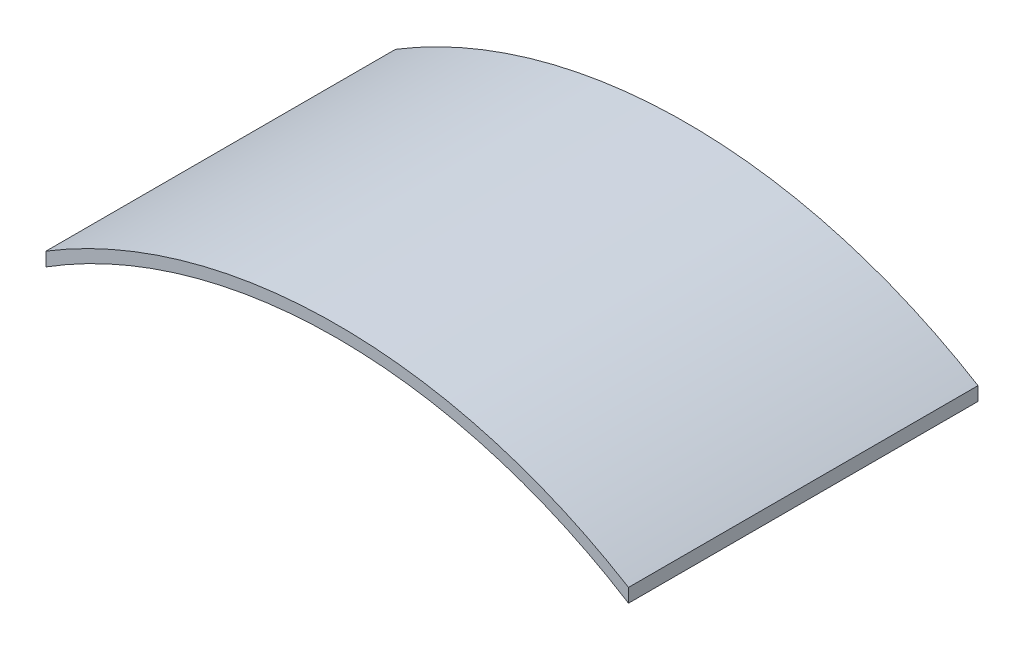
SolidWorks part; units mm, degrees
ref_plane "Front Plane" through (0, 0, 0) normal (0, 0, 1) x (1, 0, 0)
ref_plane "Top Plane" through (0, 0, 0) normal (0, 1, 0) x (1, 0, 0)
ref_plane "Right Plane" through (0, 0, 0) normal (1, 0, 0) x (0, 0, -1)
sketch "Sketch5" plane through (0, 0, 0) normal (0, 1, 0) x (1, 0, 0)
  line L1 (25, 15) -> (-25, 15)
  line L2 (25, 15) -> (25, -15)
  line L3 (25, -15) -> (-25, -15)
  line L4 (-25, 15) -> (-25, -15)
  line L5 (25, 15) -> (-25, -15) construction
  line L6 (25, -15) -> (-25, 15) construction
  point P0 (0, 0)
  dimension "D1" = 30
  dimension "D2" = 50
sketch "Sketch8" plane through (0, 0, 0) normal (0, 0, 1) x (1, 0, 0)
  circle A0 centre (0, 0) radius 50
  dimension "D1" = 100
ref_plane "Plane2" through (0, 0, 15) normal (0, 0, 1) x (1, 0, 0)
ref_plane "Plane3" through (0, 0, -15) normal (0, 0, 1) x (1, 0, 0)
curve "Curve1"
sketch "Sketch12" plane through (0, 0, 0) normal (0, 0, 1) x (1, 0, 0)
  line L0 (0, 0) -> (-84.213, 0) construction
  line L1 (16.5, 0) -> (-16.5, 0) construction
  line L2 (-84.213, 0) -> (69.4469, 0) construction
  line L3 (-48, 0) -> (-47, 0)
  line L4 (47, 0) -> (48, 0)
  arc A0 (48, 0) -> (-48, 0) centre (0, 0) ccw
  arc A1 (47, 0) -> (-47, 0) centre (0, 0) ccw
  dimension "D1" = 94
  dimension "D2" = 47
  dimension "D3" = 48
extrude "Boss-Extrude2" add sketch "Sketch12" along normal blind 30
ref_plane "Plane4" through (0, 60, 0) normal (0, 1, 0) x (1, 0, 0)
sketch "Sketch13" plane through (0, 60, 0) normal (0, 1, 0) x (1, 0, 0)
  line L0 (54.4331, -15) -> (-59.9832, -15) construction
  line L1 (-59.4484, -15) -> (59.4484, -15) construction
  line L2 (0, 0) -> (0, -33.2346) construction
  line L3 (0, -24.75) -> (0, 24.75) construction
  line L4 (-59.4484, 0) -> (59.4484, 0) construction
  line L5 (54.1202, -30) -> (-54.1202, -30)
  line L6 (54.1202, -30) -> (54.1202, 0)
  line L7 (54.1202, 0) -> (-54.1202, 0)
  line L8 (-54.1202, -30) -> (-54.1202, 0)
  line L9 (54.1202, -30) -> (-54.1202, 0) construction
  line L10 (54.1202, 0) -> (-54.1202, -30) construction
  line L12 (25, -30) -> (-25, -30)
  line L13 (25, -30) -> (25, 0)
  line L14 (25, 0) -> (-25, 0)
  line L15 (-25, -30) -> (-25, 0)
  line L16 (25, -30) -> (-25, 0) construction
  line L17 (25, 0) -> (-25, -30) construction
  point P9 (0, -15)
  point P16 (0, -15)
  dimension "D1" = 50
extrude "Cut-Extrude1" cut sketch "Sketch13" against normal blind 157 contours L13 L5 L6 L7 | L5 L15 L7 L8
